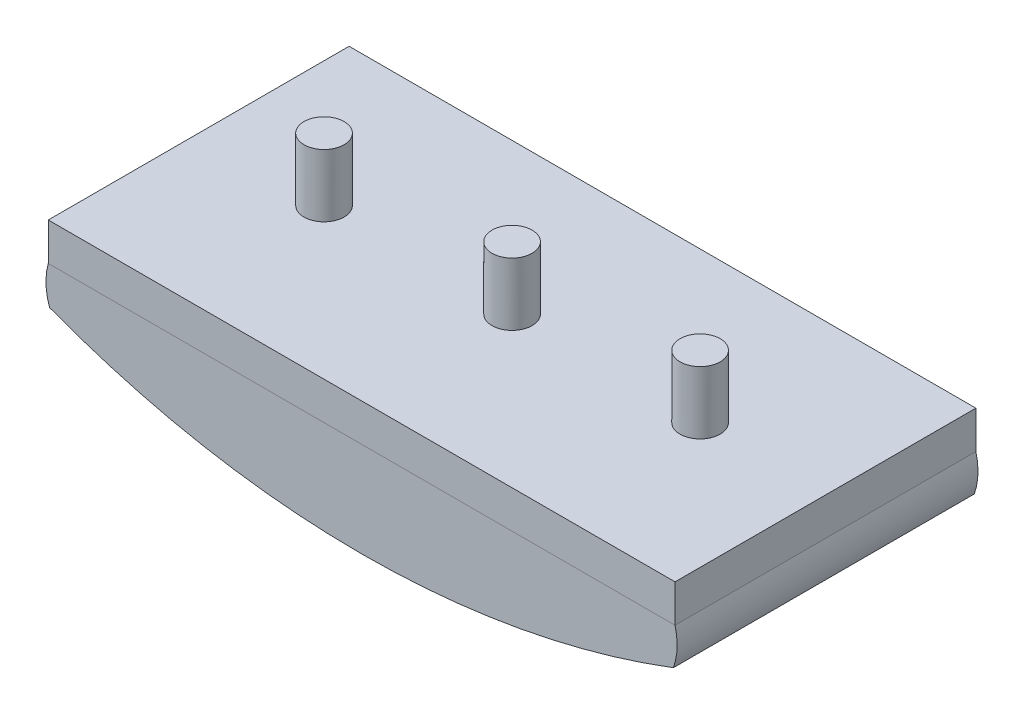
SolidWorks part; units mm, degrees
ref_plane "Front Plane" through (0, 0, 0) normal (0, 0, 1) x (1, 0, 0)
ref_plane "Top Plane" through (0, 0, 0) normal (0, 1, 0) x (1, 0, 0)
ref_plane "Right Plane" through (0, 0, 0) normal (1, 0, 0) x (0, 0, -1)
sketch "Sketch1" plane through (0, 0, 0) normal (0, 1, 0) x (1, 0, 0)
  line L1 (0, 0) -> (50, 0)
  line L2 (0, 0) -> (0, 24)
  line L3 (0, 24) -> (50, 24)
  line L4 (50, 0) -> (50, 24)
  dimension "D1" = 50
  dimension "D2" = 24
extrude "Boss-Extrude1" add sketch "Sketch1" along normal blind 3
sketch "Sketch2" plane through (0, 3, 0) normal (0, 1, 0) x (1, 0, 0)
  line L0 (25, 24) -> (25, 0) construction
  line L1 (50, 24) -> (0, 24) construction
  line L2 (0, 0) -> (50, 0) construction
  line L3 (10, 24) -> (10, 0) construction
  line L4 (40, 24) -> (40, 0) construction
  circle A0 centre (10, 12) radius 1.6
  circle A1 centre (25, 12) radius 1.6
  circle A2 centre (40, 12) radius 1.6
  dimension "D3" = 3.2
  dimension "D1" = 15
  dimension "D2" = 15
  dimension "D4" = 3
extrude "Boss-Extrude2" add sketch "Sketch2" along normal blind 5
sketch "Sketch4" plane through (0, 0, -24) normal (0, 0, -1) x (-1, 0, 0)
  line L1 (0, 0) -> (-50, 0)
  arc A15 (-50, 0) -> (-49.8671, -3) centre (-45.169, -1.2889) ccw
  arc A17 (-0.102, -3) -> (-49.8671, -3) centre (-24.9845, 62.4283) cw
  arc A18 (0, 0) -> (-0.102, -3) centre (-4.8176, -1.338) cw
  dimension "D2" = 5
  dimension "D3" = 5
  dimension "D4" = 3
  dimension "D5" = 70
  dimension "D1" = 3
extrude "Boss-Extrude3" add sketch "Sketch4" against normal blind 24 separate body
